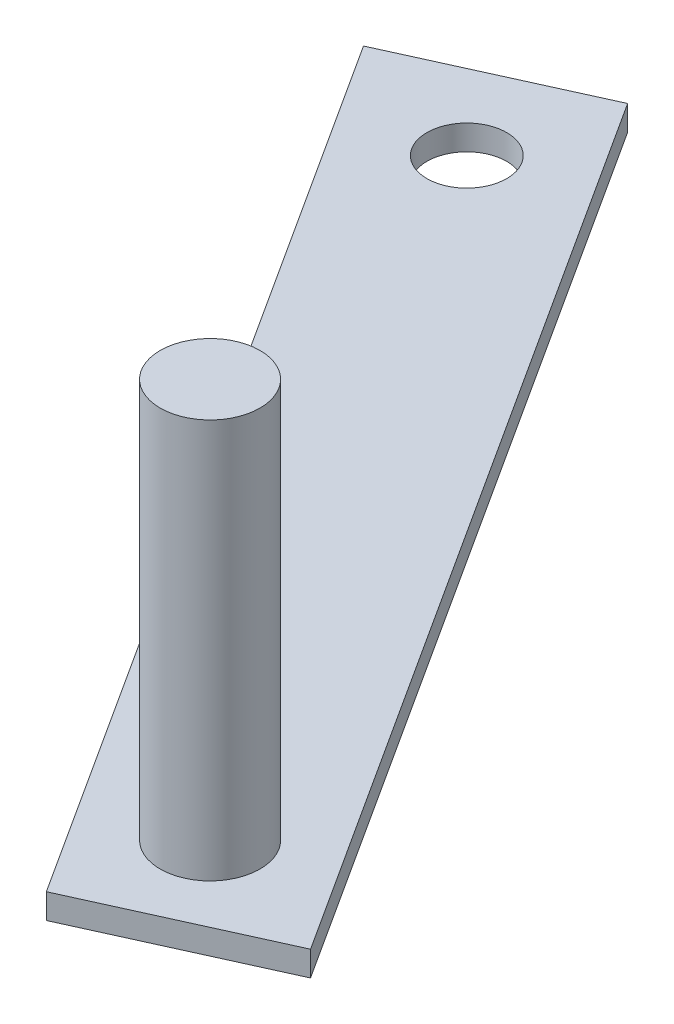
SolidWorks part; units mm, degrees
ref_plane "Front" through (0, 0, 0) normal (0, 0, 1) x (1, 0, 0)
ref_plane "Top" through (0, 0, 0) normal (0, 1, 0) x (1, 0, 0)
ref_plane "Right" through (0, 0, 0) normal (1, 0, 0) x (0, 0, -1)
sketch "Sketch1" plane through (0, 0, 0) normal (0, 1, 0) x (1, 0, 0)
  line L0 (-55.441, -40.2685) -> (-128.4608, 73.101)
  line L1 (-128.4608, 73.101) -> (-105.3198, 83.5727)
  line L2 (-105.3198, 83.5727) -> (-32.3001, -29.7967)
  line L3 (-32.3001, -29.7967) -> (-55.441, -40.2685)
  circle A0 centre (-109.8116, 67.6003) radius 5.0783
  dimension "D1" = 25.4
  dimension "D2" = 25.4
  dimension "D3" = 134.85
  dimension "D4" = 12.7
  dimension "D5" = 12.7
extrude "Boss-Extrude1" add sketch "Sketch1" along normal blind 3.175
sketch "Sketch2" plane through (0, 3.175, 0) normal (0, 1, 0) x (1, 0, 0)
  line L0 (-55.441, -40.2685) -> (-32.3001, -29.7967) construction
  line L2 (-128.4608, 73.101) -> (-55.441, -40.2685) construction
  circle A0 centre (-50.6961, -24.1815) radius 6.35
  dimension "D1" = 12.7
  dimension "D2" = 12.7
  dimension "D3" = 12.7
extrude "Boss-Extrude2" add sketch "Sketch2" along normal blind 50.8
